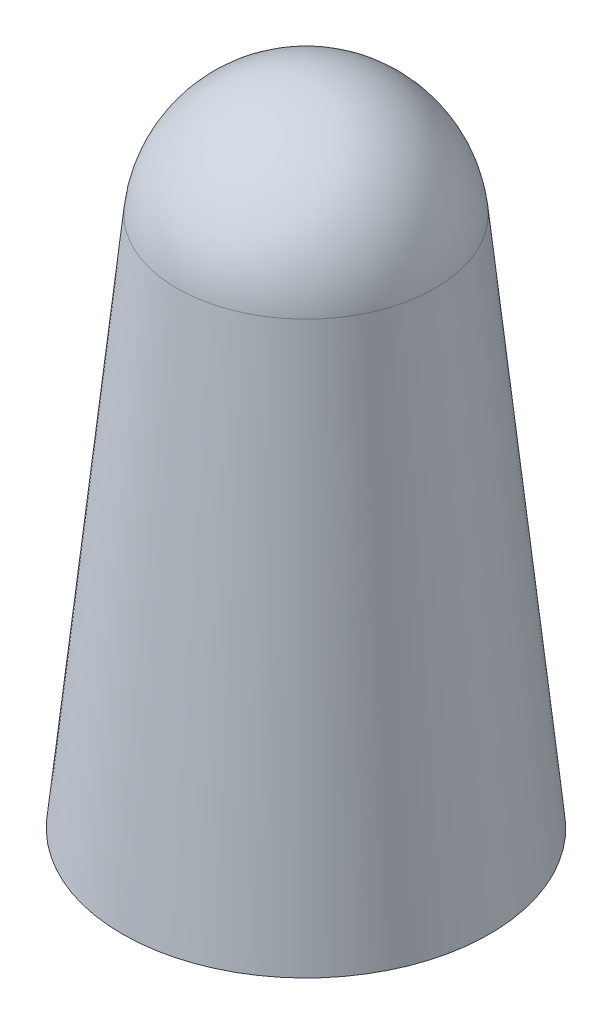
SolidWorks part; units mm, degrees
ref_plane "Plan de face" through (0, 0, 0) normal (0, 0, 1) x (1, 0, 0)
ref_plane "Plan de dessus" through (0, 0, 0) normal (0, 1, 0) x (1, 0, 0)
ref_plane "Plan de droite" through (0, 0, 0) normal (1, 0, 0) x (0, 0, -1)
sketch "Esquisse1" plane through (0, 0, 0) normal (0, 0, 1) x (1, 0, 0)
  line L0 (-2.5, 0) -> (-4.25, 0)
  line L1 (-2.5, 0) -> (-2.5, 6)
  line L2 (-2.5, 6) -> (-2, 6)
  line L3 (0, 14) -> (0, 15)
  line L4 (-4.25, 0) -> (-2.9843, 12.3069)
  line L5 (0, 0) -> (0, 18.5309) construction
  line L6 (-2, 6) -> (-2, 12)
  arc A0 (0, 15) -> (-2.9843, 12.3069) centre (0, 12) ccw
  arc A1 (0, 14) -> (-2, 12) centre (0, 12) ccw
  dimension "D1" = 3
  dimension "D2" = 5
  dimension "D3" = 6
  dimension "D4" = 8.5
  dimension "D5" = 15
  dimension "D6" = 1
revolve "Révolution1" add sketch "Esquisse1" angle 360 about L5
